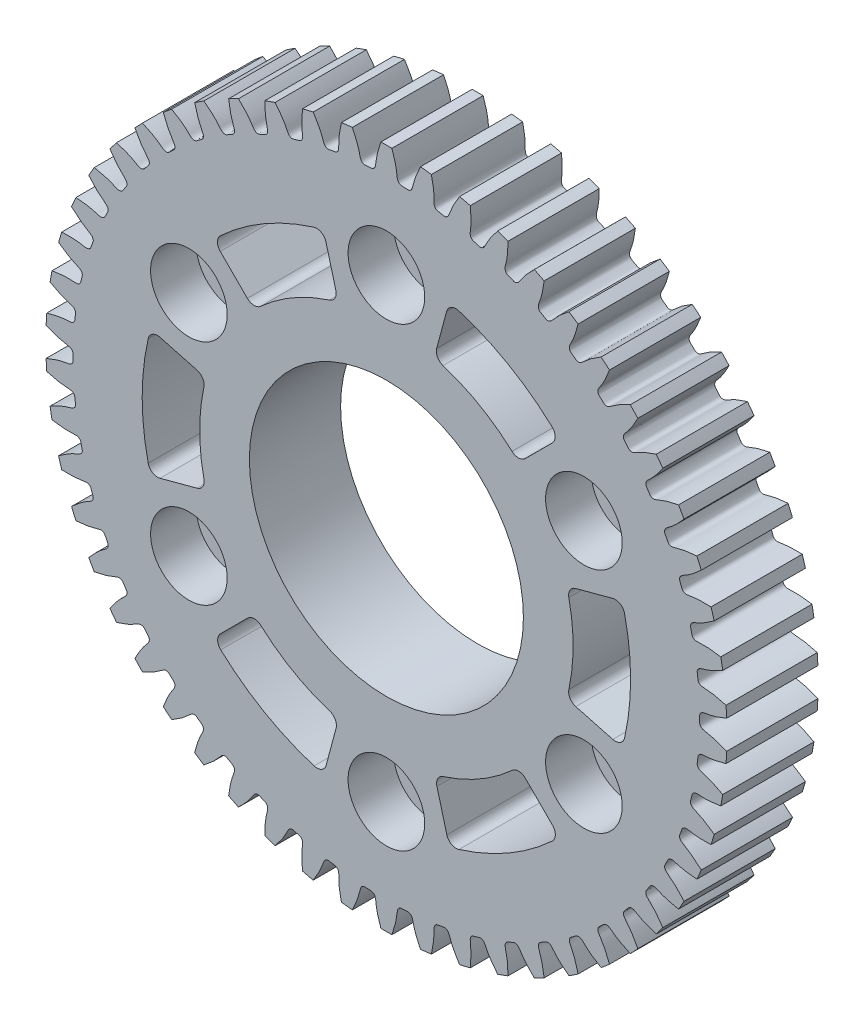
SolidWorks part; units mm, degrees
material "7075-T6 (SN)"
ref_plane "Front Plane" through (0, 0, 0) normal (0, 0, 1) x (1, 0, 0)
ref_plane "Top Plane" through (0, 0, 0) normal (0, 1, 0) x (1, 0, 0)
ref_plane "Right Plane" through (0, 0, 0) normal (1, 0, 0) x (0, 0, -1)
ref_plane "Plane1" through (0, 0, 4.7625) normal (0, 0, 1) x (1, 0, 0)
sketch "Sketch1" plane through (0, 0, 4.7625) normal (0, 0, 1) x (1, 0, 0)
  arc A0 (35.1151, 5.6076) -> (34.9153, 6.7406) centre (0, 0) ccw
  arc A1 (34.2266, 9.6463) -> (33.8967, 10.7484) centre (0, 0) ccw
  arc A2 (32.8753, 13.5546) -> (32.4197, 14.6109) centre (0, 0) ccw
  arc A3 (31.0794, 17.2795) -> (30.5042, 18.2758) centre (0, 0) ccw
  arc A4 (28.8633, 20.7708) -> (28.1763, 21.6936) centre (0, 0) ccw
  arc A5 (26.2568, 23.9812) -> (25.4673, 24.818) centre (0, 0) ccw
  arc A6 (23.2952, 26.8672) -> (22.4139, 27.6067) centre (0, 0) ccw
  arc A7 (20.0186, 29.39) -> (19.0574, 30.0221) centre (0, 0) ccw
  arc A8 (16.4712, 31.5153) -> (15.4432, 32.0316) centre (0, 0) ccw
  arc A9 (12.7012, 33.2144) -> (11.6201, 33.6078) centre (0, 0) ccw
  arc A10 (8.7593, 34.4643) -> (7.6399, 34.7296) centre (0, 0) ccw
  arc A11 (4.6991, 35.2482) -> (3.5564, 35.3817) centre (0, 0) ccw
  arc A12 (0.5752, 35.5553) -> (-0.5752, 35.5553) centre (0, 0) ccw
  arc A13 (-3.5564, 35.3817) -> (-4.6991, 35.2482) centre (0, 0) ccw
  arc A14 (-7.6399, 34.7296) -> (-8.7593, 34.4643) centre (0, 0) ccw
  arc A15 (-11.6201, 33.6078) -> (-12.7012, 33.2144) centre (0, 0) ccw
  arc A16 (-15.4432, 32.0316) -> (-16.4712, 31.5153) centre (0, 0) ccw
  arc A17 (-19.0574, 30.0221) -> (-20.0186, 29.39) centre (0, 0) ccw
  arc A18 (-22.4139, 27.6067) -> (-23.2952, 26.8672) centre (0, 0) ccw
  arc A19 (-25.4673, 24.818) -> (-26.2568, 23.9812) centre (0, 0) ccw
  arc A20 (-28.1763, 21.6936) -> (-28.8633, 20.7708) centre (0, 0) ccw
  arc A21 (-30.5042, 18.2758) -> (-31.0794, 17.2795) centre (0, 0) ccw
  arc A22 (-32.4197, 14.6109) -> (-32.8753, 13.5546) centre (0, 0) ccw
  arc A23 (-33.8967, 10.7484) -> (-34.2266, 9.6463) centre (0, 0) ccw
  arc A24 (-34.9153, 6.7406) -> (-35.1151, 5.6076) centre (0, 0) ccw
  arc A25 (-35.4617, 2.6416) -> (-35.5286, 1.4931) centre (0, 0) ccw
  arc A26 (-35.5286, -1.4931) -> (-35.4617, -2.6416) centre (0, 0) ccw
  arc A27 (-35.1151, -5.6076) -> (-34.9153, -6.7406) centre (0, 0) ccw
  arc A28 (-34.2266, -9.6463) -> (-33.8967, -10.7484) centre (0, 0) ccw
  arc A29 (-32.8753, -13.5546) -> (-32.4197, -14.6109) centre (0, 0) ccw
  arc A30 (-31.0794, -17.2795) -> (-30.5042, -18.2758) centre (0, 0) ccw
  arc A31 (-28.8633, -20.7708) -> (-28.1763, -21.6936) centre (0, 0) ccw
  arc A32 (-26.2568, -23.9812) -> (-25.4673, -24.818) centre (0, 0) ccw
  arc A33 (-23.2952, -26.8672) -> (-22.4139, -27.6067) centre (0, 0) ccw
  arc A34 (-20.0186, -29.39) -> (-19.0574, -30.0221) centre (0, 0) ccw
  arc A35 (-16.4712, -31.5153) -> (-15.4432, -32.0316) centre (0, 0) ccw
  arc A36 (-12.7012, -33.2144) -> (-11.6201, -33.6078) centre (0, 0) ccw
  arc A37 (-8.7593, -34.4643) -> (-7.6399, -34.7296) centre (0, 0) ccw
  arc A38 (-4.6991, -35.2482) -> (-3.5564, -35.3817) centre (0, 0) ccw
  arc A39 (-0.5752, -35.5553) -> (0.5752, -35.5553) centre (0, 0) ccw
  arc A40 (3.5564, -35.3817) -> (4.6991, -35.2482) centre (0, 0) ccw
  arc A41 (7.6399, -34.7296) -> (8.7593, -34.4643) centre (0, 0) ccw
  arc A42 (11.6201, -33.6078) -> (12.7012, -33.2144) centre (0, 0) ccw
  arc A43 (15.4432, -32.0316) -> (16.4712, -31.5153) centre (0, 0) ccw
  arc A44 (19.0574, -30.0221) -> (20.0186, -29.39) centre (0, 0) ccw
  arc A45 (22.4139, -27.6067) -> (23.2952, -26.8672) centre (0, 0) ccw
  arc A46 (25.4673, -24.818) -> (26.2568, -23.9812) centre (0, 0) ccw
  arc A47 (28.1763, -21.6936) -> (28.8633, -20.7708) centre (0, 0) ccw
  arc A48 (30.5042, -18.2758) -> (31.0794, -17.2795) centre (0, 0) ccw
  arc A49 (32.4197, -14.6109) -> (32.8753, -13.5546) centre (0, 0) ccw
  arc A50 (33.8967, -10.7484) -> (34.2266, -9.6463) centre (0, 0) ccw
  arc A51 (34.9153, -6.7406) -> (35.1151, -5.6076) centre (0, 0) ccw
  arc A52 (35.4617, -2.6416) -> (35.5286, -1.4931) centre (0, 0) ccw
  arc A53 (35.5286, 1.4931) -> (35.4617, 2.6416) centre (0, 0) ccw
  spline S0 degree 3 number of poles 69 (35.4617, 2.6416) -> (35.1151, 5.6076)
  spline S1 degree 3 number of poles 69 (34.9153, 6.7406) -> (34.2266, 9.6463)
  spline S2 degree 3 number of poles 69 (33.8967, 10.7484) -> (32.8753, 13.5546)
  spline S3 degree 3 number of poles 69 (32.4197, 14.6109) -> (31.0794, 17.2795)
  spline S4 degree 3 number of poles 69 (30.5042, 18.2758) -> (28.8633, 20.7708)
  spline S5 degree 3 number of poles 69 (28.1763, 21.6936) -> (26.2568, 23.9812)
  spline S6 degree 3 number of poles 69 (25.4673, 24.818) -> (23.2952, 26.8672)
  spline S7 degree 3 number of poles 69 (22.4139, 27.6067) -> (20.0186, 29.39)
  spline S8 degree 3 number of poles 69 (19.0574, 30.0221) -> (16.4712, 31.5153)
  spline S9 degree 3 number of poles 69 (15.4432, 32.0316) -> (12.7012, 33.2144)
  spline S10 degree 3 number of poles 69 (11.6201, 33.6078) -> (8.7593, 34.4643)
  spline S11 degree 3 number of poles 69 (7.6399, 34.7296) -> (4.6991, 35.2482)
  spline S12 degree 3 number of poles 69 (3.5564, 35.3817) -> (0.5752, 35.5553)
  spline S13 degree 3 number of poles 69 (-0.5752, 35.5553) -> (-3.5564, 35.3817)
  spline S14 degree 3 number of poles 69 (-4.6991, 35.2482) -> (-7.6399, 34.7296)
  spline S15 degree 3 number of poles 69 (-8.7593, 34.4643) -> (-11.6201, 33.6078)
  spline S16 degree 3 number of poles 69 (-12.7012, 33.2144) -> (-15.4432, 32.0316)
  spline S17 degree 3 number of poles 69 (-16.4712, 31.5153) -> (-19.0574, 30.0221)
  spline S18 degree 3 number of poles 69 (-20.0186, 29.39) -> (-22.4139, 27.6067)
  spline S19 degree 3 number of poles 69 (-23.2952, 26.8672) -> (-25.4673, 24.818)
  spline S20 degree 3 number of poles 69 (-26.2568, 23.9812) -> (-28.1763, 21.6936)
  spline S21 degree 3 number of poles 69 (-28.8633, 20.7708) -> (-30.5042, 18.2758)
  spline S22 degree 3 number of poles 69 (-31.0794, 17.2795) -> (-32.4197, 14.6109)
  spline S23 degree 3 number of poles 69 (-32.8753, 13.5546) -> (-33.8967, 10.7484)
  spline S24 degree 3 number of poles 69 (-34.2266, 9.6463) -> (-34.9153, 6.7406)
  spline S25 degree 3 number of poles 69 (-35.1151, 5.6076) -> (-35.4617, 2.6416)
  spline S26 degree 3 number of poles 69 (-35.5286, 1.4931) -> (-35.5286, -1.4931)
  spline S27 degree 3 number of poles 69 (-35.4617, -2.6416) -> (-35.1151, -5.6076)
  spline S28 degree 3 number of poles 69 (-34.9153, -6.7406) -> (-34.2266, -9.6463)
  spline S29 degree 3 number of poles 69 (-33.8967, -10.7484) -> (-32.8753, -13.5546)
  spline S30 degree 3 number of poles 69 (-32.4197, -14.6109) -> (-31.0794, -17.2795)
  spline S31 degree 3 number of poles 69 (-30.5042, -18.2758) -> (-28.8633, -20.7708)
  spline S32 degree 3 number of poles 69 (-28.1763, -21.6936) -> (-26.2568, -23.9812)
  spline S33 degree 3 number of poles 69 (-25.4673, -24.818) -> (-23.2952, -26.8672)
  spline S34 degree 3 number of poles 69 (-22.4139, -27.6067) -> (-20.0186, -29.39)
  spline S35 degree 3 number of poles 69 (-19.0574, -30.0221) -> (-16.4712, -31.5153)
  spline S36 degree 3 number of poles 69 (-15.4432, -32.0316) -> (-12.7012, -33.2144)
  spline S37 degree 3 number of poles 69 (-11.6201, -33.6078) -> (-8.7593, -34.4643)
  spline S38 degree 3 number of poles 69 (-7.6399, -34.7296) -> (-4.6991, -35.2482)
  spline S39 degree 3 number of poles 69 (-3.5564, -35.3817) -> (-0.5752, -35.5553)
  spline S40 degree 3 number of poles 69 (0.5752, -35.5553) -> (3.5564, -35.3817)
  spline S41 degree 3 number of poles 69 (4.6991, -35.2482) -> (7.6399, -34.7296)
  spline S42 degree 3 number of poles 69 (8.7593, -34.4643) -> (11.6201, -33.6078)
  spline S43 degree 3 number of poles 69 (12.7012, -33.2144) -> (15.4432, -32.0316)
  spline S44 degree 3 number of poles 69 (16.4712, -31.5153) -> (19.0574, -30.0221)
  spline S45 degree 3 number of poles 69 (20.0186, -29.39) -> (22.4139, -27.6067)
  spline S46 degree 3 number of poles 69 (23.2952, -26.8672) -> (25.4673, -24.818)
  spline S47 degree 3 number of poles 69 (26.2568, -23.9812) -> (28.1763, -21.6936)
  spline S48 degree 3 number of poles 69 (28.8633, -20.7708) -> (30.5042, -18.2758)
  spline S49 degree 3 number of poles 69 (31.0794, -17.2795) -> (32.4197, -14.6109)
  spline S50 degree 3 number of poles 69 (32.8753, -13.5546) -> (33.8967, -10.7484)
  spline S51 degree 3 number of poles 69 (34.2266, -9.6463) -> (34.9153, -6.7406)
  spline S52 degree 3 number of poles 69 (35.1151, -5.6076) -> (35.4617, -2.6416)
  spline S53 degree 3 number of poles 69 (35.5286, -1.4931) -> (35.5286, 1.4931)
extrude "Boss-Extrude1" add sketch "Sketch1" against normal blind 9.525
sketch "Sketch2" plane through (0, 0, 4.7625) normal (0, 0, 1) x (1, 0, 0)
  line L0 (-5.0224, 18.8421) -> (-6.5753, 24.6377)
  line L1 (-18.0671, 17.9953) -> (-13.8245, 13.7526)
  arc A0 (-13.8245, 13.7526) -> (-5.0224, 18.8421) centre (0, 0) cw
  arc A1 (-6.5753, 24.6377) -> (-18.0671, 17.9953) centre (0, 0) ccw
extrude "Cut-Extrude1" cut sketch "Sketch2" against normal through all
sketch "Sketch3" plane through (0, 0, 4.7625) normal (0, 0, 1) x (1, 0, 0)
  line L0 (-18.829, 5.0715) -> (-24.6245, 6.6244)
  line L1 (-24.6179, -6.6489) -> (-18.8223, -5.096)
  arc A0 (-18.8223, -5.096) -> (-18.829, 5.0715) centre (0, 0) cw
  arc A1 (-24.6245, 6.6244) -> (-24.6179, -6.6489) centre (0, 0) ccw
extrude "Cut-Extrude2" cut sketch "Sketch3" against normal through all
sketch "Sketch4" plane through (0, 0, 4.7625) normal (0, 0, 1) x (1, 0, 0)
  line L0 (-13.8065, -13.7706) -> (-18.0492, -18.0133)
  line L1 (-6.5508, -24.6442) -> (-4.9979, -18.8486)
  arc A0 (-4.9979, -18.8486) -> (-13.8065, -13.7706) centre (0, 0) cw
  arc A1 (-18.0492, -18.0133) -> (-6.5508, -24.6442) centre (0, 0) ccw
extrude "Cut-Extrude3" cut sketch "Sketch4" against normal through all
sketch "Sketch5" plane through (0, 0, 4.7625) normal (0, 0, 1) x (1, 0, 0)
  line L0 (5.0224, -18.8421) -> (6.5753, -24.6377)
  line L1 (18.0671, -17.9953) -> (13.8245, -13.7526)
  arc A0 (13.8245, -13.7526) -> (5.0224, -18.8421) centre (0, 0) cw
  arc A1 (6.5753, -24.6377) -> (18.0671, -17.9953) centre (0, 0) ccw
extrude "Cut-Extrude4" cut sketch "Sketch5" against normal through all
sketch "Sketch6" plane through (0, 0, 4.7625) normal (0, 0, 1) x (1, 0, 0)
  line L0 (13.8065, 13.7706) -> (18.0492, 18.0133)
  line L1 (6.5508, 24.6442) -> (4.9979, 18.8486)
  arc A0 (4.9979, 18.8486) -> (13.8065, 13.7706) centre (0, 0) cw
  arc A1 (18.0492, 18.0133) -> (6.5508, 24.6442) centre (0, 0) ccw
extrude "Cut-Extrude5" cut sketch "Sketch6" against normal through all
sketch "Sketch7" plane through (0, 0, -4.7625) normal (0, 0, -1) x (-1, 0, 0)
  line L0 (-24.6245, -6.6244) -> (-18.829, -5.0715)
  line L1 (-18.8223, 5.096) -> (-24.6179, 6.6489)
  arc A0 (-24.6179, 6.6489) -> (-24.6245, -6.6244) centre (0, 0) ccw
  arc A1 (-18.829, -5.0715) -> (-18.8223, 5.096) centre (0, 0) cw
extrude "Cut-Extrude6" cut sketch "Sketch7" against normal through all
hole_wizard "M25 Clearance Hole1" positions "Sketch9" profile "Sketch8" hole size "M25" standard "ANSI Metric"
sketch "Sketch9" plane through (0, 0, 4.7625) normal (0, 0, 1) x (1, 0, 0)
  point P0 (0, 0)
sketch "Sketch8" plane through (0, 0, 4.7625) normal (1, 0, 0) x (0, -1, 0)
  line L0 (0, 0) -> (0, 9.525)
  line L1 (0, 9.525) -> (14.3065, 9.525)
  line L2 (14.3065, 9.525) -> (14.3065, 0)
  line L5 (14.3065, 0) -> (0, 0)
  line L11 (0, -6.35) -> (0, 107.95) construction
  dimension "Thru Hole Dia." = 28.6131
  dimension "Thru Hole Depth" = 9.525
hole_wizard "CBORE for M4 Hex Head Machine Screw1" positions "Sketch11" profile "Sketch10" counterbore size "M4" standard "ANSI Metric"
sketch "Sketch11" plane through (0, 0, 4.7625) normal (0, 0, 1) x (1, 0, 0)
  point P0 (-20.6222, 11.9062)
  point P1 (-20.6222, -11.9063)
  point P2 (0, -23.8125)
  point P3 (20.6222, -11.9062)
  point P4 (20.6222, 11.9063)
  point P5 (0, 23.8125)
sketch "Sketch10" plane through (-20.6222, 11.9062, 4.7625) normal (1, 0, 0) x (0, -1, 0)
  line L0 (0, 0) -> (0, 9.525)
  line L1 (0, 9.525) -> (2.15, 9.525)
  line L3 (2.15, 9.525) -> (2.15, 4.7625)
  line L4 (2.15, 4.7625) -> (4, 4.7625)
  line L5 (4, 4.7625) -> (4, 0)
  line L7 (4, 0) -> (0, 0)
  line L11 (0, -6.35) -> (0, 107.95) construction
  dimension "Thru Hole Dia." = 4.3
  dimension "Thru Hole Depth" = 9.525
  dimension "C'Bore Dia." = 8
  dimension "C'Bore Depth" = 4.7625
fillet "Fillet1" radius 1 24 edges at (-18.829, 5.0715, 0) (5.0224, -18.8421, 0) (-13.8065, -13.7706, 0) (24.6245, -6.6244, 0) (-24.6245, 6.6244, 0) (18.829, -5.0715, 0) (-18.0492, -18.0133, 0) (18.8223, 5.096, 0) (6.5753, -24.6377, 0) (6.5508, 24.6442, 0) (-24.6179, -6.6489, 0) (18.0492, 18.0133, 0) (-18.8223, -5.096, 0) (4.9979, 18.8486, 0) (-6.5508, -24.6442, 0) (13.8065, 13.7706, 0) (-4.9979, -18.8486, 0) (-18.0671, 17.9953, 0) (18.0671, -17.9953, 0) (-6.5753, 24.6377, 0) (13.8245, -13.7526, 0) (-13.8245, 13.7526, 0) (24.6179, 6.6489, 0) (-5.0224, 18.8421, 0)
